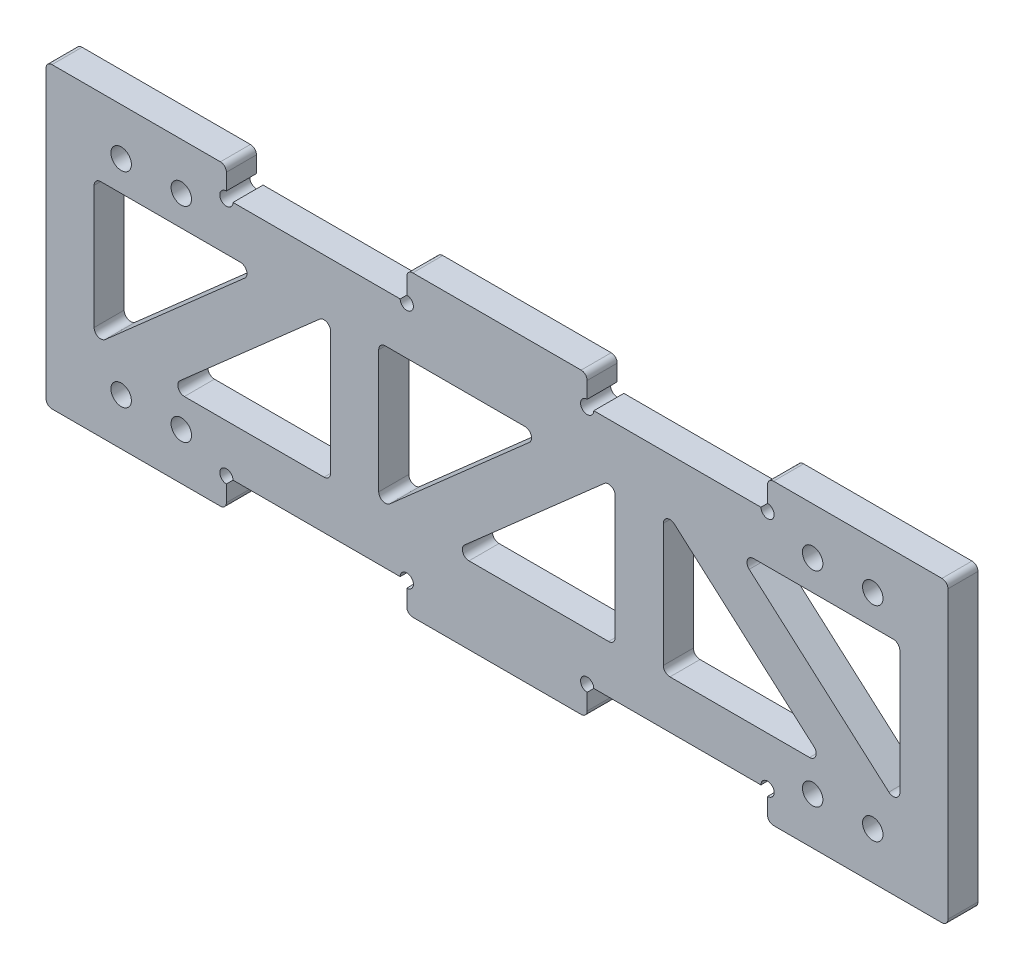
SolidWorks part; units mm, degrees
material "Thornel Mat VMA"
ref_plane "前视基准面" through (0, 0, 0) normal (0, 0, 1) x (1, 0, 0)
ref_plane "上视基准面" through (0, 0, 0) normal (0, 1, 0) x (1, 0, 0)
ref_plane "右视基准面" through (0, 0, 0) normal (1, 0, 0) x (0, 0, -1)
other "Configuration Table"
sketch "草图1" plane through (0, 0, 0) normal (0, 0, 1) x (1, 0, 0)
  line L1 (0, 0) -> (150, 0)
  line L2 (0, 0) -> (0, 40)
  line L3 (0, 40) -> (150, 40)
  line L4 (150, 0) -> (150, 40)
  dimension "D1" = 150
  dimension "D2" = 40
extrude "凸台-拉伸1" add sketch "草图1" along normal blind 5
sketch "草图2" plane through (0, 0, 5) normal (0, 0, 1) x (1, 0, 0)
  line L0 (150, 40) -> (0, 40) construction
  line L1 (0, 40) -> (30, 40)
  line L2 (0, 40) -> (0, 44.8)
  line L3 (0, 44.8) -> (30, 44.8)
  line L4 (30, 40) -> (30, 44.8)
  line L5 (60, 40) -> (90, 40)
  line L6 (60, 40) -> (60, 44.8)
  line L7 (60, 44.8) -> (90, 44.8)
  line L8 (90, 40) -> (90, 44.8)
  line L9 (0, 0) -> (150, 0) construction
  line L10 (150, 40) -> (120, 40)
  line L11 (150, 40) -> (150, 44.8)
  line L12 (150, 44.8) -> (120, 44.8)
  line L13 (120, 40) -> (120, 44.8)
  line L14 (0, 0) -> (30, 0)
  line L15 (0, 0) -> (0, -4.8)
  line L16 (0, -4.8) -> (30, -4.8)
  line L17 (30, 0) -> (30, -4.8)
  line L18 (60, 0) -> (90, 0)
  line L19 (60, 0) -> (60, -4.8)
  line L20 (60, -4.8) -> (90, -4.8)
  line L21 (90, 0) -> (90, -4.8)
  line L22 (150, 0) -> (150, 40) construction
  line L23 (120, 0) -> (150, 0)
  line L24 (120, 0) -> (120, -4.8)
  line L25 (120, -4.8) -> (150, -4.8)
  line L26 (150, 0) -> (150, -4.8)
  line L27 (30, 44.8) -> (60, 44.8) construction
  line L28 (90, 44.8) -> (120, 44.8) construction
  line L29 (30, -4.8) -> (60, -4.8) construction
  line L30 (90, -4.8) -> (120, -4.8) construction
  dimension "D1" = 4.8
  dimension "D2" = 4.8
extrude "凸台-拉伸2" add sketch "草图2" against normal blind 5
sketch "草图3" plane through (0, 0, 5) normal (0, 0, 1) x (1, 0, 0)
  circle A0 centre (30, 40) radius 1.1
  circle A1 centre (60, 40) radius 1.1
  circle A2 centre (90, 40) radius 1.1
  circle A3 centre (120, 40) radius 1.1
  circle A4 centre (30, 0) radius 1.1
  circle A5 centre (60, 0) radius 1.1
  circle A6 centre (90, 0) radius 1.1
  circle A7 centre (120, 0) radius 1.1
  dimension "D1" = 2.2
extrude "切除-拉伸1" cut sketch "草图3" against normal blind 5
fillet "圆角1" radius 1 12 edges at (150, 44.8, 2.5) (120, 44.8, 2.5) (90, 44.8, 2.5) (60, 44.8, 2.5) (30, 44.8, 2.5) (0, 44.8, 2.5) (150, -4.8, 2.5) (120, -4.8, 2.5) (90, -4.8, 2.5) (60, -4.8, 2.5) (30, -4.8, 2.5) (0, -4.8, 2.5)
sketch "草图5" plane through (0, 0, 0) normal (0, 0, -1) x (-1, 0, 0)
  line L12 (-118.9, 40) -> (-150, 40)
  line L13 (-150, -3.8) -> (-150, 43.8) construction
  line L14 (-118.9, 32) -> (-142, 32)
  line L15 (-150, 40) -> (0, 40)
  line L16 (-150, 40) -> (-150, 0)
  line L17 (-150, 0) -> (0, 0)
  line L18 (0, 40) -> (0, 0)
  line L19 (-142, 32) -> (-8, 32)
  line L20 (-8, 32) -> (-8, 8)
  line L21 (-142, 8) -> (-8, 8)
  line L22 (-142, 32) -> (-142, 8)
  line L23 (-118.9, 32) -> (-150, 32) construction
  line L24 (-142, 8) -> (-114.7665, 32)
  line L25 (-8, 8) -> (-35.2335, 32)
  line L26 (-94.6667, 32) -> (-94.6667, 8)
  line L27 (-102.6667, 32) -> (-102.6667, 8)
  line L28 (-82.5668, 32) -> (-55.3333, 8)
  line L29 (-55.3333, 8) -> (-55.3333, 32)
  line L30 (-129.9001, 8) -> (-102.6667, 8)
  line L31 (-102.6667, 32) -> (-129.9001, 8)
  line L32 (-94.6667, 32) -> (-67.4332, 8)
  line L33 (-47.3333, 32) -> (-47.3333, 8)
  line L34 (-47.3333, 32) -> (-20.0999, 8)
  line L35 (-94.6667, 8) -> (-67.4332, 8)
  line L36 (-47.3333, 8) -> (-20.0999, 8)
  dimension "D2" = 8
  dimension "D3" = 8
  dimension "D4" = 8
  dimension "D5" = 8
  dimension "D6" = 8
  dimension "D1" = 8
extrude "切除-拉伸2" cut sketch "草图5" against normal blind 10 contours L22 L24 L19 L14 | L27 L31 L21 | L32 L26 L21 | L25 L20 L19 | L28 L29 L19 | L34 L33 L21
fillet "圆角2" radius 1.1 18 edges at (8, 8, 2.5) (8, 32, 2.5) (35.2335, 32, 2.5) (67.4332, 8, 2.5) (94.6667, 8, 2.5) (94.6667, 32, 2.5) (102.6667, 8, 2.5) (129.9001, 8, 2.5) (102.6667, 32, 2.5) (142, 8, 2.5) (114.7665, 32, 2.5) (142, 32, 2.5) (20.0999, 8, 2.5) (47.3333, 8, 2.5) (47.3333, 32, 2.5) (55.3333, 32, 2.5) (82.5668, 32, 2.5) (55.3333, 8, 2.5)
hole_wizard "M3 间隙孔1" positions "草图6" profile "草图7" hole size "M3" standard "GB" end condition through all
sketch "草图6" plane through (0, 0, 0) normal (0, 0, -1) x (-1, 0, 0)
  line L0 (0, 43.8) -> (0, -3.8) construction
  line L1 (-29, 44.8) -> (-1, 44.8) construction
  point P0 (-137.5, 37)
  point P3 (-127.5, 37)
  point P6 (-22.5, 37)
  point P9 (-12.5, 37)
  point P12 (-137.5, 3)
  point P15 (-127.5, 3)
  point P18 (-22.5, 3)
  point P21 (-12.5, 3)
  dimension "D1" = 12.5
  dimension "D2" = 22.5
  dimension "D3" = 127.5
  dimension "D4" = 137.5
  dimension "D5" = 7.8
  dimension "D6" = 41.8
sketch "草图7" plane through (137.5, 37, 0) normal (1, 0, 0) x (0, 1, 0)
  line L0 (0, 0) -> (0, 5)
  line L1 (0, 5) -> (1.7, 5)
  line L2 (1.7, 5) -> (1.7, 0)
  line L5 (1.7, 0) -> (0, 0)
  line L11 (0, -6.35) -> (0, 107.95) construction
  dimension "通孔孔直径" = 3.4
  dimension "通孔孔深度" = 5
